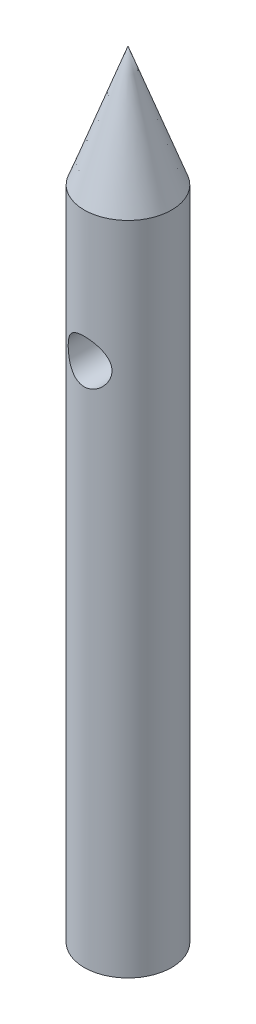
SolidWorks part; units mm, degrees
ref_plane "Front Plane" through (0, 0, 0) normal (0, 0, 1) x (1, 0, 0)
ref_plane "Top Plane" through (0, 0, 0) normal (0, 1, 0) x (1, 0, 0)
ref_plane "Right Plane" through (0, 0, 0) normal (1, 0, 0) x (0, 0, -1)
sketch "Sketch1" plane through (0, 0, 0) normal (0, 1, 0) x (1, 0, 0)
  circle A0 centre (0, 0) radius 2
  dimension "D1" = 4
extrude "Boss-Extrude1" add sketch "Sketch1" along normal blind 30
cosmetic thread "Cosmetic Thread1" parameters "D1"=7, "D2"=2.439
sketch "Sketch7" plane through (0, 30, 0) normal (0, 1, 0) x (1, 0, 0)
  circle A0 centre (0, 0) radius 2 construction
  circle A1 centre (0, 0) radius 2
extrude "Boss-Extrude2" add sketch "Sketch7" along normal blind 7 draft 20 separate body
ref_plane "Plane2" through (0, 30, 0) normal (0, 1, 0) x (1, 0, 0)
hole_wizard "Ø2.0mm Dowel Hole1" positions "3DSketch7" profile "Sketch21" hole size "Ø2.0" standard "ISO"
sketch3d "3DSketch7"
  point P0 (0, 24, 2)
  dimension "D1" = 0
  dimension "D2" = 6
sketch "Sketch21" plane through (0, 24, 2) normal (1, 0, 0) x (0, -1, 0)
  line L0 (0, 0) -> (0, 4)
  line L1 (0, 4) -> (1, 4)
  line L2 (1, 4) -> (1, 0)
  line L5 (1, 0) -> (0, 0)
  line L11 (0, -6.35) -> (0, 107.95) construction
  dimension "Thru Hole Dia." = 2
  dimension "Thru Hole Depth" = 4
